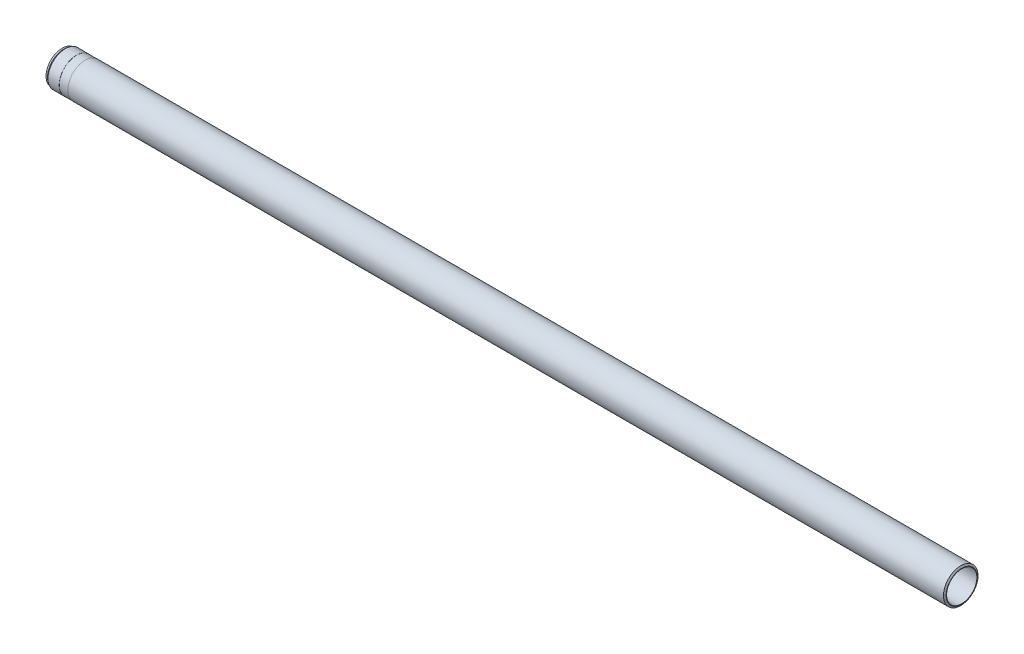
SolidWorks part; units mm, degrees
ref_plane "Front" through (0, 0, 0) normal (0, 0, 1) x (1, 0, 0)
ref_plane "Top" through (0, 0, 0) normal (0, 1, 0) x (1, 0, 0)
ref_plane "Right" through (0, 0, 0) normal (1, 0, 0) x (0, 0, -1)
sketch "Sketch1" plane through (0, 0, 0) normal (0, 0, 1) x (1, 0, 0)
  line L0 (-122.7842, 0) -> (99.5499, 0) construction
  line L1 (0, 35) -> (0, 36)
  line L2 (0, 36) -> (-2.3094, 40)
  line L3 (-2.3094, 40) -> (-2028, 40)
  line L4 (-2028, 40) -> (-2028, 39.75)
  line L5 (-2028, 39.75) -> (-2048, 39.75)
  line L6 (-2048, 39.75) -> (-2048, 40)
  line L7 (-2048, 40) -> (-2073.9296, 40)
  line L8 (-2073.9296, 40) -> (-2077.5, 37.5)
  line L9 (-2077.5, 37.5) -> (-2081, 37.5)
  line L10 (-2081, 37.5) -> (-2081, 35.7274)
  line L11 (-2081, 35.7274) -> (-2080, 35.15)
  line L12 (-2080, 35.15) -> (-2066, 35.15)
  line L13 (-2066, 35.15) -> (-2065.7402, 35)
  line L14 (-2065.7402, 35) -> (0, 35)
  dimension "D1" = 2081
  dimension "D2" = 80
  dimension "D3" = 70
  dimension "D4" = 70.3
  dimension "D5" = 75
  dimension "D6" = 72
  dimension "D7" = 60
  dimension "D8" = 79.5
  dimension "D9" = 3.5
  dimension "D10" = 35
  dimension "D11" = 30
  dimension "D12" = 1
  dimension "D13" = 30
  dimension "D14" = 15
  dimension "D15" = 33
  dimension "D16" = 20
revolve "Base-Revolve" add sketch "Sketch1" angle 360 about L0
